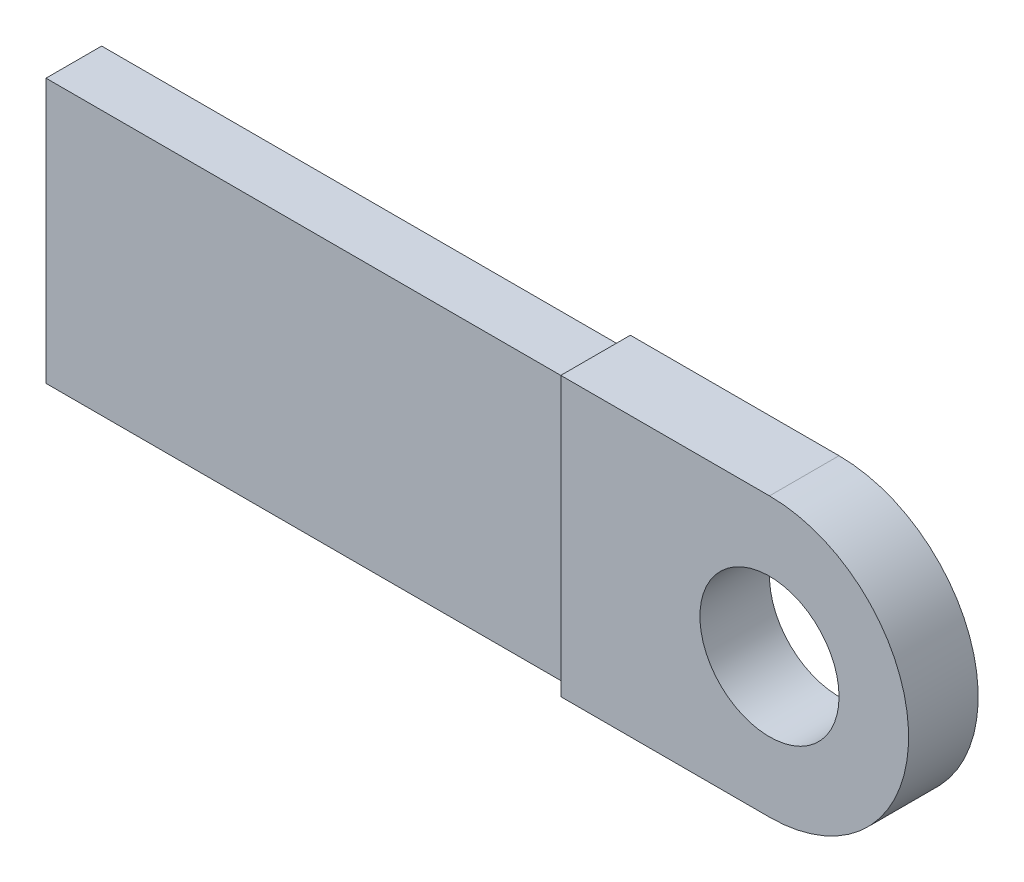
SolidWorks part; units mm, degrees
material "AISI 304"
ref_plane "Front Plane" through (0, 0, 0) normal (0, 0, 1) x (1, 0, 0)
ref_plane "Top Plane" through (0, 0, 0) normal (0, 1, 0) x (1, 0, 0)
ref_plane "Right Plane" through (0, 0, 0) normal (1, 0, 0) x (0, 0, -1)
sketch "Sketch1" plane through (0, 0, 0) normal (0, 0, 1) x (1, 0, 0)
  line L1 (0, 0) -> (100, 0)
  line L2 (0, 0) -> (0, 80)
  line L3 (0, 80) -> (100, 80)
  line L4 (100, 0) -> (100, 80)
  arc A0 (60, 80) -> (60, 0) centre (60, 40) cw
  point P8 (111.5218, 80)
  dimension "D1" = 80
  dimension "D2" = 100
extrude "Boss-Extrude1" add sketch "Sketch1" along normal blind 20 contours A0 L3 L2 L1
sketch "Sketch2" plane through (0, 0, 20) normal (0, 0, 1) x (1, 0, 0)
  circle A0 centre (60, 40) radius 20
  arc A1 (60, 0) -> (60, 80) centre (60, 40) ccw construction
  dimension "D1" = 40
extrude "Cut-Extrude1" cut sketch "Sketch2" against normal through all
sketch "Sketch3" plane through (0, 0, 0) normal (-1, 0, 0) x (0, 0, 1)
  line L12 (2, 78) -> (2, 2)
  line L13 (2, 2) -> (18, 2)
  line L14 (18, 2) -> (18, 78)
  line L15 (18, 78) -> (2, 78)
  line L16 (2, 78) -> (2, 2)
  line L17 (2, 2) -> (18, 2)
  line L18 (18, 2) -> (18, 78)
  line L19 (18, 78) -> (2, 78)
  dimension "D1" = 2
extrude "Boss-Extrude2" add sketch "Sketch3" along normal blind 150
